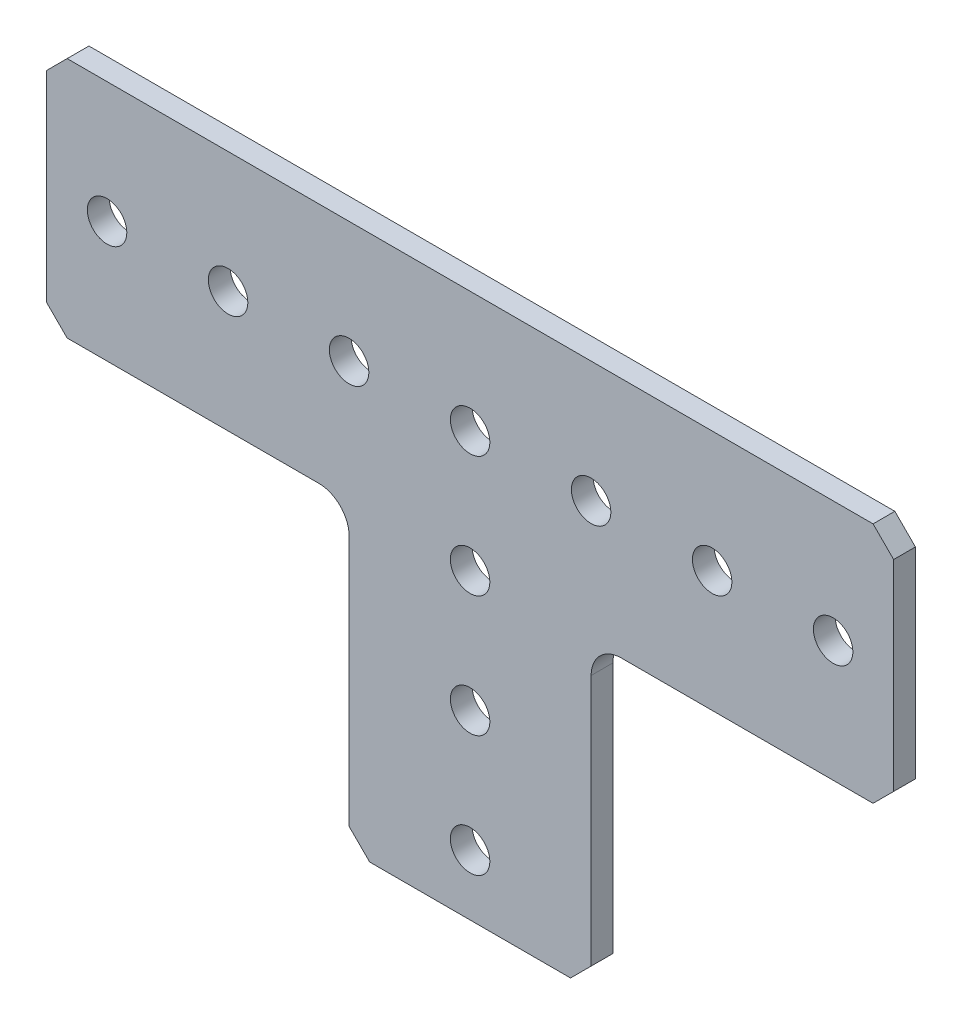
SolidWorks part; units mm, degrees
ref_plane "Front Plane" through (0, 0, 0) normal (0, 0, 1) x (1, 0, 0)
ref_plane "Top Plane" through (0, 0, 0) normal (0, 1, 0) x (1, 0, 0)
ref_plane "Right Plane" through (0, 0, 0) normal (1, 0, 0) x (0, 0, -1)
ref_plane "Plane1" through (0, 0, 0) normal (0, 0, -1) x (-1, 0, 0)
sketch "Sketch1" plane through (0, 0, 0) normal (0, 0, -1) x (-1, 0, 0)
  line L0 (-12.7, -29.591) -> (-10.541, -31.75)
  line L1 (-10.541, -31.75) -> (10.541, -31.75)
  line L2 (10.541, -31.75) -> (12.7, -29.591)
  line L3 (12.7, -29.591) -> (12.7, -3.175)
  line L4 (15.875, 0) -> (42.291, 0)
  line L5 (42.291, 0) -> (44.45, 2.159)
  line L6 (44.45, 2.159) -> (44.45, 23.241)
  line L7 (44.45, 23.241) -> (42.291, 25.4)
  line L8 (42.291, 25.4) -> (-42.291, 25.4)
  line L9 (-42.291, 25.4) -> (-44.45, 23.241)
  line L10 (-44.45, 23.241) -> (-44.45, 2.159)
  line L11 (-44.45, 2.159) -> (-42.291, 0)
  line L12 (-42.291, 0) -> (-15.875, 0)
  line L13 (-12.7, -3.175) -> (-12.7, -29.591)
  circle A0 centre (0, -12.7) radius 2.0701
  circle A1 centre (-38.1, 12.7) radius 2.0701
  circle A2 centre (-12.7, 12.7) radius 2.0701
  circle A3 centre (12.7, 12.7) radius 2.0701
  circle A4 centre (25.4, 12.7) radius 2.0701
  arc A5 (12.7, -3.175) -> (15.875, 0) centre (15.875, -3.175) cw
  arc A6 (-15.875, 0) -> (-12.7, -3.175) centre (-15.875, -3.175) cw
  circle A7 centre (38.1, 12.7) radius 2.0701
  circle A8 centre (0, -25.4) radius 2.0701
  circle A9 centre (0, 12.7) radius 2.0701
  circle A10 centre (-25.4, 12.7) radius 2.0701
  circle A11 centre (0, 0) radius 2.0701
extrude "Boss-Extrude1" add sketch "Sketch1" against normal blind 2.286
